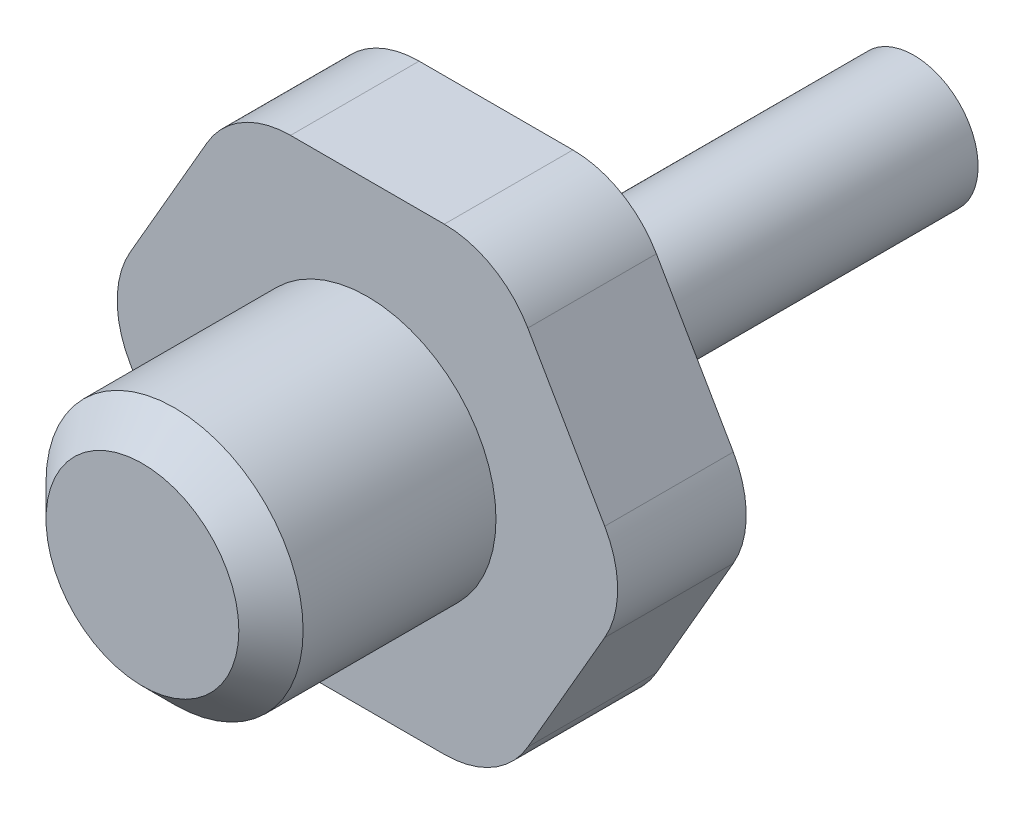
SolidWorks part; units mm, degrees
material "Alloy Steel (SS)"
ref_plane "Front Plane" through (0, 0, 0) normal (0, 0, 1) x (1, 0, 0)
ref_plane "Top Plane" through (0, 0, 0) normal (0, 1, 0) x (1, 0, 0)
ref_plane "Right Plane" through (0, 0, 0) normal (1, 0, 0) x (0, 0, -1)
sketch "Sketch1" plane through (0, 0, 0) normal (0, 0, 1) x (1, 0, 0)
  line L1 (8.2489, 0) -> (4.1244, 7.1438)
  line L2 (4.1244, 7.1438) -> (-4.1244, 7.1438)
  line L3 (-4.1244, 7.1438) -> (-8.2489, 0)
  line L4 (-8.2489, 0) -> (-4.1244, -7.1438)
  line L5 (-4.1244, -7.1438) -> (4.1244, -7.1438)
  line L6 (4.1244, -7.1438) -> (8.2489, 0)
  circle A0 centre (0, 0) radius 7.1438 construction
  dimension "D1" = 14.2875
extrude "Boss-Extrude1" add sketch "Sketch1" along normal blind 4
sketch "Sketch2" plane through (0, 0, 4) normal (0, 0, 1) x (1, 0, 0)
  circle A0 centre (0, 0) radius 4
  dimension "D1" = 8
extrude "Boss-Extrude2" add sketch "Sketch2" along normal blind 7
chamfer "Chamfer1" distance 1 angle 45 1 edges at (4, 0, 11)
sketch "Sketch3" plane through (0, 0, 0) normal (0, 0, -1) x (-1, 0, 0)
  circle A0 centre (0, 0) radius 2.375
  dimension "D1" = 4.75
extrude "Boss-Extrude3" add sketch "Sketch3" along normal blind 3
sketch "Sketch4" plane through (0, 0, -3) normal (0, 0, -1) x (-1, 0, 0)
  circle A0 centre (0, 0) radius 2
  dimension "D1" = 4
extrude "Boss-Extrude4" add sketch "Sketch4" along normal blind 10
fillet "Fillet2" radius 3 6 edges at (4.1244, -7.1438, 2) (8.2489, 0, 2) (-4.1244, -7.1438, 2) (-8.2489, 0, 2) (-4.1244, 7.1438, 2) (4.1244, 7.1438, 2)
fillet "Fillet3" radius 1 1 edges at (2.375, 0, 0)
